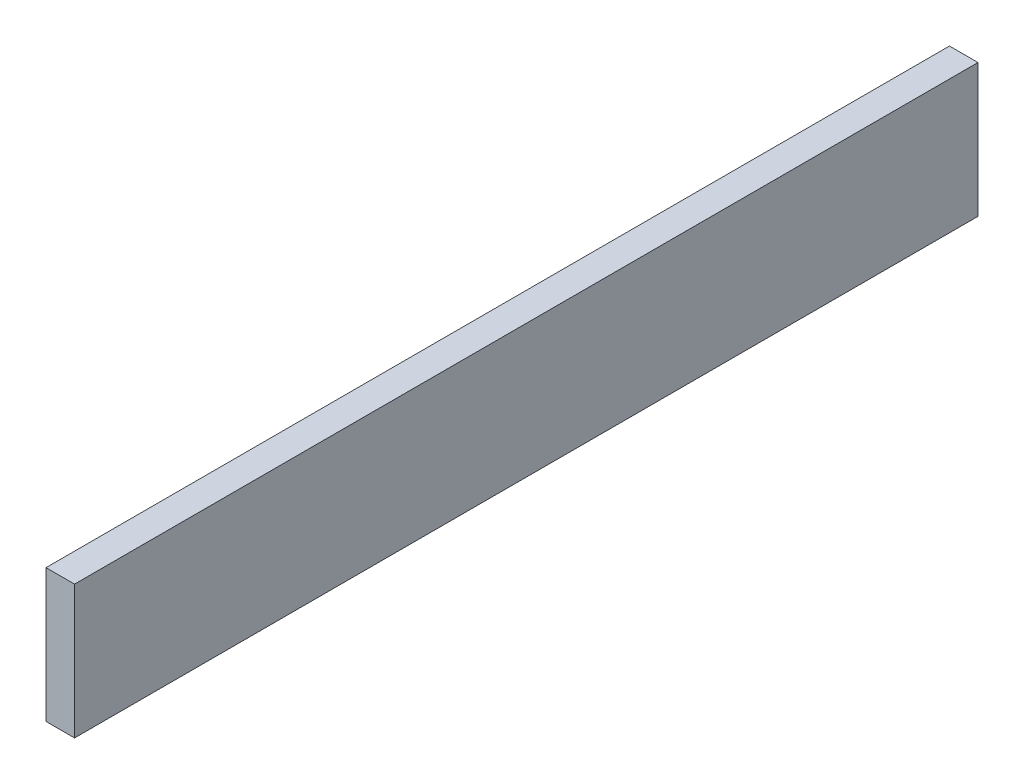
SolidWorks part; units mm, degrees
material "Pine"
ref_plane "Front Plane" through (0, 0, 0) normal (0, 0, 1) x (1, 0, 0)
ref_plane "Top Plane" through (0, 0, 0) normal (0, 1, 0) x (1, 0, 0)
ref_plane "Right Plane" through (0, 0, 0) normal (1, 0, 0) x (0, 0, -1)
sketch "Sketch1" plane through (0, 0, 0) normal (1, 0, 0) x (0, 0, -1)
  line L1 (-301.397, -44.45) -> (301.397, -44.45)
  line L2 (-301.397, -44.45) -> (-301.397, 44.45)
  line L3 (-301.397, 44.45) -> (301.397, 44.45)
  line L4 (301.397, -44.45) -> (301.397, 44.45)
  line L5 (-301.397, -44.45) -> (301.397, 44.45) construction
  line L6 (-301.397, 44.45) -> (301.397, -44.45) construction
  point P0 (0, 0)
  dimension "D1" = 88.9
  dimension "D2" = 602.7941
extrude "Boss-Extrude1" add sketch "Sketch1" along normal blind 19.05
equation "\"D1@Sketch1\"=3.5in"
equation "\"D2@Sketch1\"=2ft-2*.5in/tan(75)"
equation "\"D1@Boss-Extrude1\"=.75in"
